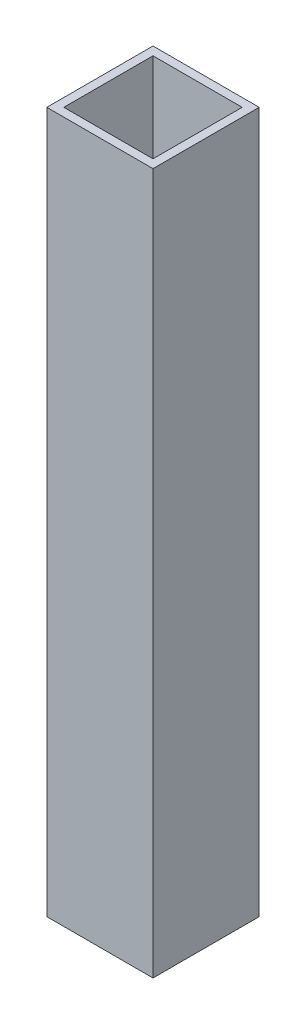
SolidWorks part; units mm, degrees
ref_plane "Front Plane" through (0, 0, 0) normal (0, 0, 1) x (1, 0, 0)
ref_plane "Top Plane" through (0, 0, 0) normal (0, 1, 0) x (1, 0, 0)
ref_plane "Right Plane" through (0, 0, 0) normal (1, 0, 0) x (0, 0, -1)
sketch "Sketch1" plane through (0, 0, 0) normal (0, 1, 0) x (1, 0, 0)
  line L0 (-12.5, 12.5) -> (12.5, -12.5) construction
  line L1 (-12.5, 12.5) -> (12.5, 12.5)
  line L2 (-12.5, 12.5) -> (-12.5, -12.5)
  line L3 (-12.5, -12.5) -> (12.5, -12.5)
  line L4 (12.5, 12.5) -> (12.5, -12.5)
  line L5 (-10.5, 10.5) -> (10.5, 10.5)
  line L6 (10.5, 10.5) -> (10.5, -10.5)
  line L7 (-10.5, -10.5) -> (10.5, -10.5)
  line L8 (-10.5, 10.5) -> (-10.5, -10.5)
  dimension "D1" = 25
  dimension "D2" = 2
extrude "Boss-Extrude1" add sketch "Sketch1" along normal blind 165
